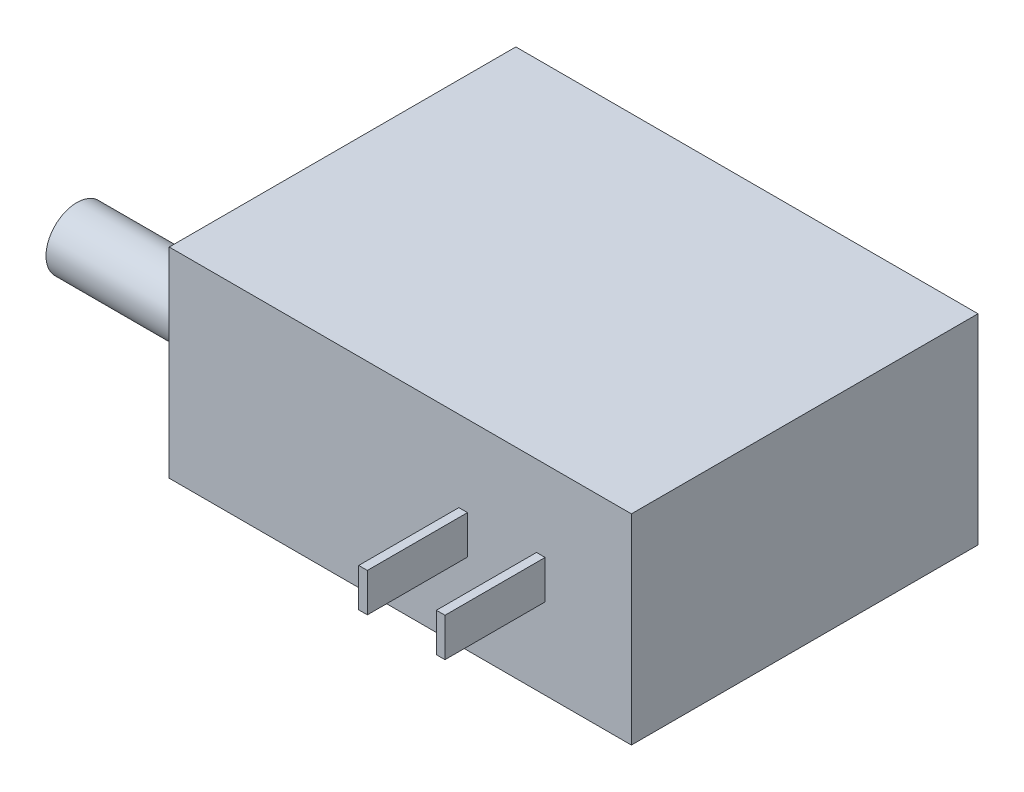
SolidWorks part; units mm, degrees
material "Delrin 2700 NC010, Low Viscosity Acetal Copolymer (SS)"
ref_plane "Front Plane" through (0, 0, 0) normal (0, 0, 1) x (1, 0, 0)
ref_plane "Top Plane" through (0, 0, 0) normal (0, 1, 0) x (1, 0, 0)
ref_plane "Right Plane" through (0, 0, 0) normal (1, 0, 0) x (0, 0, -1)
sketch "Sketch1" plane through (0, 0, 0) normal (0, 1, 0) x (1, 0, 0)
  line L0 (-38.1, 28.575) -> (38.1, -28.575) construction
  line L1 (-38.1, 28.575) -> (38.1, 28.575)
  line L2 (-38.1, 28.575) -> (-38.1, -28.575)
  line L3 (-38.1, -28.575) -> (38.1, -28.575)
  line L4 (38.1, 28.575) -> (38.1, -28.575)
  dimension "D1" = 76.2
  dimension "D2" = 57.15
extrude "Boss-Extrude1" add sketch "Sketch1" along normal blind 33.02
sketch "Sketch2" plane through (-38.1, 0, 0) normal (-1, 0, 0) x (0, 0, 1)
  line L0 (28.575, 33.02) -> (28.575, 0) construction
  line L1 (18.415, 33.02) -> (18.415, 0) construction
  line L2 (-28.575, 33.02) -> (28.575, 33.02) construction
  line L3 (-28.575, 0) -> (28.575, 0) construction
  circle A0 centre (18.415, 16.51) radius 5.08
  dimension "D1" = 10.16
  dimension "D2" = 10.16
extrude "Boss-Extrude2" add sketch "Sketch2" along normal blind 25.4
sketch "Sketch3" plane through (0, 0, 28.575) normal (0, 0, 1) x (1, 0, 0)
  line L0 (38.1, 33.02) -> (38.1, 0) construction
  line L1 (23.876, 19.685) -> (22.4536, 19.685)
  line L2 (23.876, 19.685) -> (23.876, 13.335)
  line L3 (23.876, 13.335) -> (22.4536, 13.335)
  line L4 (22.4536, 19.685) -> (22.4536, 13.335)
  line L5 (11.0744, 19.685) -> (9.652, 19.685)
  line L6 (11.0744, 19.685) -> (11.0744, 13.335)
  line L7 (11.0744, 13.335) -> (9.652, 13.335)
  line L8 (9.652, 19.685) -> (9.652, 13.335)
  line L9 (9.652, 19.685) -> (9.652, 33.02) construction
  line L10 (-38.1, 33.02) -> (38.1, 33.02) construction
  line L11 (9.652, 13.335) -> (9.652, 0) construction
  line L12 (-38.1, 0) -> (38.1, 0) construction
  dimension "D1" = 14.224
  dimension "D2" = 14.224
  dimension "D3" = 1.4224
  dimension "D4" = 6.35
extrude "Boss-Extrude3" add sketch "Sketch3" along normal blind 16.51
